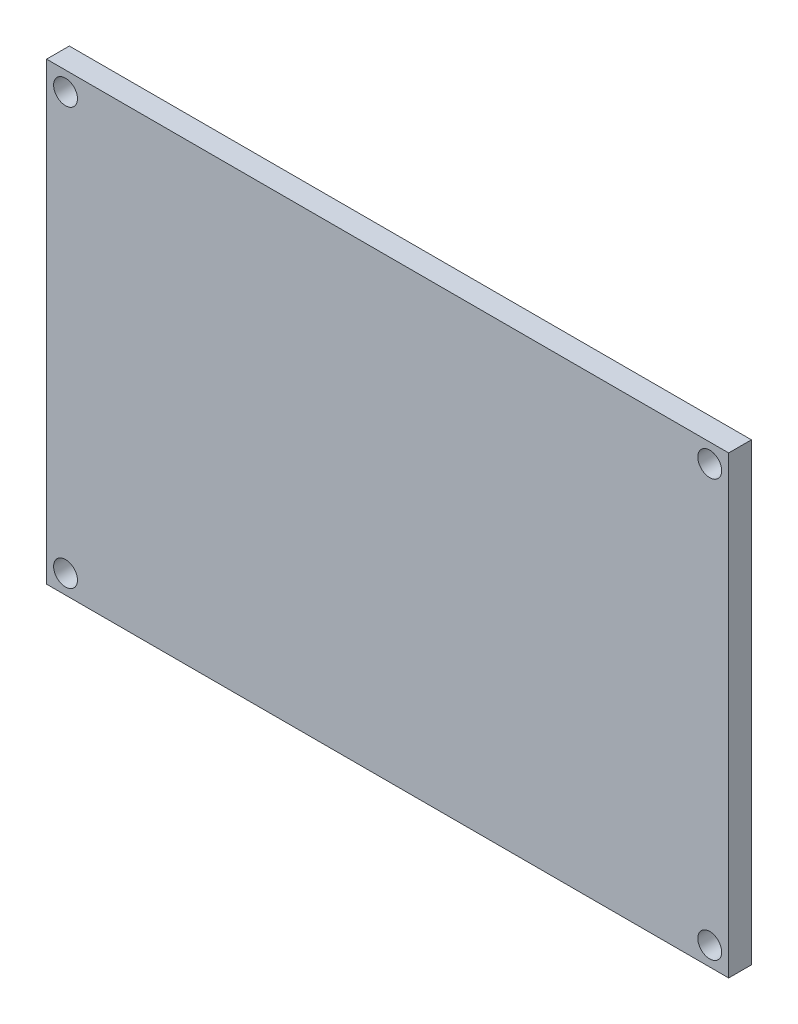
SolidWorks part; units mm, degrees
ref_plane "Front Plane" through (0, 0, 0) normal (0, 0, 1) x (1, 0, 0)
ref_plane "Top Plane" through (0, 0, 0) normal (0, 1, 0) x (1, 0, 0)
ref_plane "Right Plane" through (0, 0, 0) normal (1, 0, 0) x (0, 0, -1)
sketch "Sketch1" plane through (0, 0, 0) normal (0, 0, 1) x (1, 0, 0)
  line L1 (-45, 30) -> (45, 30)
  line L2 (-45, 30) -> (-45, -30)
  line L3 (-45, -30) -> (45, -30)
  line L4 (45, 30) -> (45, -30)
  circle A0 centre (-42.5, 27.5) radius 1.575
  circle A1 centre (42.5, 27.5) radius 1.575
  circle A2 centre (-42.5, -27.5) radius 1.575
  circle A3 centre (42.5, -27.5) radius 1.575
  point P0 (0, 0)
  dimension "D5" = 3.15
  dimension "D1" = 90
  dimension "D2" = 60
  dimension "D3" = 2.5
  dimension "D4" = 2.5
  dimension "D6" = 2.5
  dimension "D7" = 2.5
  dimension "D8" = 2.5
  dimension "D9" = 2.5
  dimension "D10" = 2.5
  dimension "D11" = 2.5
extrude "Boss-Extrude1" add sketch "Sketch1" along normal blind 3
